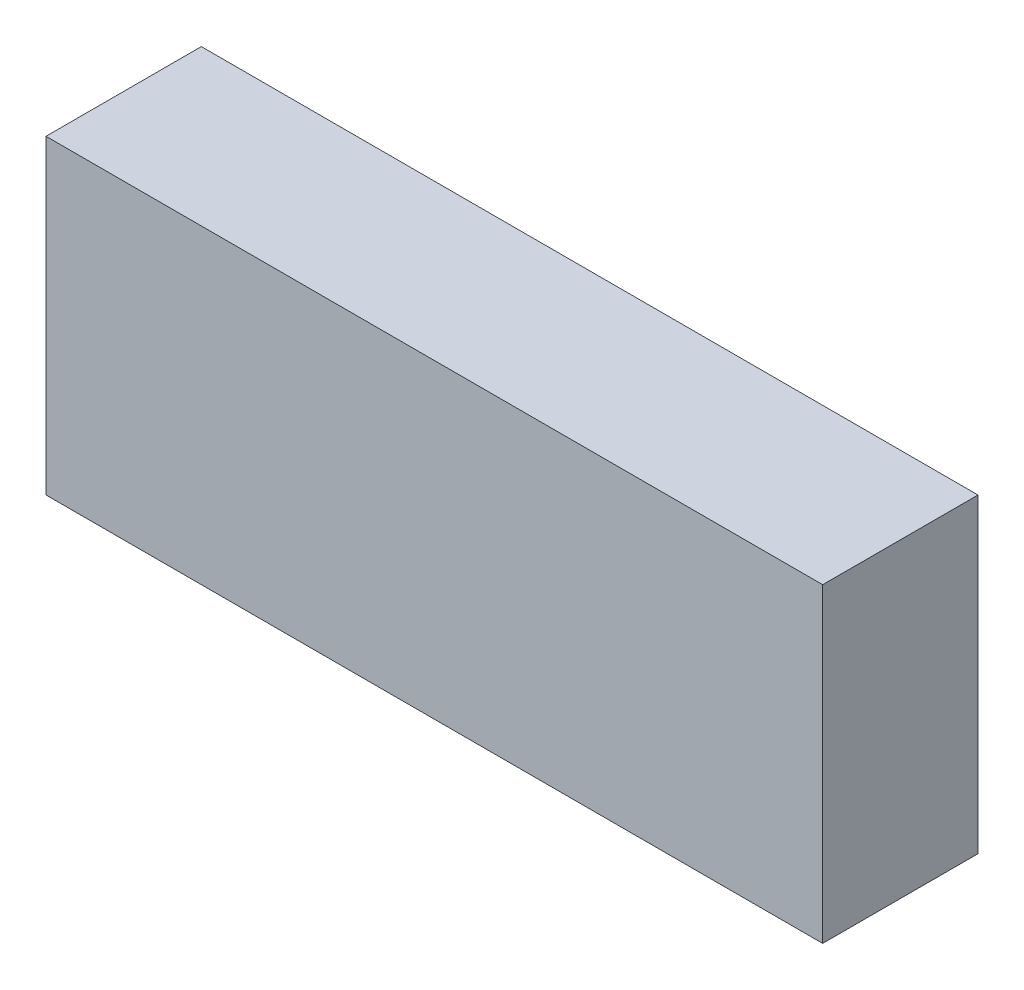
SolidWorks part; units mm, degrees
ref_plane "Plan de face" through (0, 0, 0) normal (0, 0, 1) x (1, 0, 0)
ref_plane "Plan de dessus" through (0, 0, 0) normal (0, 1, 0) x (1, 0, 0)
ref_plane "Plan de droite" through (0, 0, 0) normal (1, 0, 0) x (0, 0, -1)
sketch "Esquisse1" plane through (0, 0, 0) normal (0, 0, 1) x (1, 0, 0)
  line L1 (0, 0) -> (45, 0)
  line L2 (0, 0) -> (0, 18)
  line L3 (0, 18) -> (45, 18)
  line L4 (45, 0) -> (45, 18)
  dimension "D1" = 45
  dimension "D2" = 18
extrude "Boss.-Extru.1" add sketch "Esquisse1" along normal blind 9
